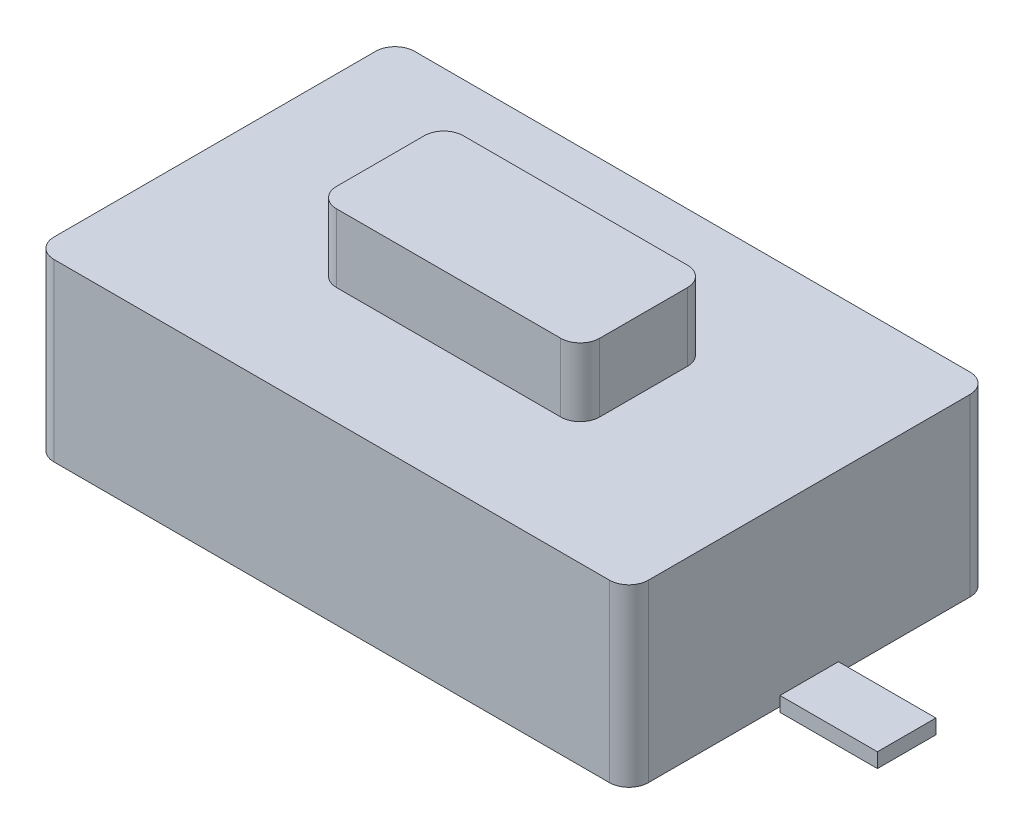
SolidWorks part; units mm, degrees
ref_plane "Спереди" through (0, 0, 0) normal (0, 0, 1) x (1, 0, 0)
ref_plane "Сверху" through (0, 0, 0) normal (0, 1, 0) x (1, 0, 0)
ref_plane "Справа" through (0, 0, 0) normal (1, 0, 0) x (0, 0, -1)
other "Configuration Table"
sketch "Эскиз1" plane through (0, 0, 0) normal (0, 1, 0) x (1, 0, 0)
  line L1 (-3.05, -1.85) -> (3.05, -1.85)
  line L2 (-3.05, -1.85) -> (-3.05, 1.85)
  line L3 (-3.05, 1.85) -> (3.05, 1.85)
  line L4 (3.05, -1.85) -> (3.05, 1.85)
  line L5 (-3.05, -1.85) -> (3.05, 1.85) construction
  line L6 (-3.05, 1.85) -> (3.05, -1.85) construction
  point P0 (0, 0)
  dimension "D1" = 6.1
  dimension "D2" = 3.7
extrude "Бобышка-Вытянуть1" add sketch "Эскиз1" along normal blind 1.8
sketch "Эскиз3" plane through (0, 1.8, 0) normal (0, 1, 0) x (1, 0, 0)
  line L1 (-1.35, -0.65) -> (1.35, -0.65)
  line L2 (-1.35, -0.65) -> (-1.35, 0.65)
  line L3 (-1.35, 0.65) -> (1.35, 0.65)
  line L4 (1.35, -0.65) -> (1.35, 0.65)
  line L5 (-1.35, -0.65) -> (1.35, 0.65) construction
  line L6 (-1.35, 0.65) -> (1.35, -0.65) construction
  point P0 (0, 0)
  dimension "D1" = 2.7
  dimension "D2" = 1.3
extrude "Бобышка-Вытянуть2" add sketch "Эскиз3" along normal blind 0.7
sketch "Эскиз4" plane through (0, 0, 0) normal (0, -1, 0) x (1, 0, 0)
  line L0 (-3.05, -1.85) -> (-3.05, 1.85) construction
  line L1 (-3.05, 0.3) -> (-4.05, 0.3)
  line L2 (-3.05, 0.3) -> (-3.05, -0.3)
  line L3 (-3.05, -0.3) -> (-4.05, -0.3)
  line L4 (-4.05, 0.3) -> (-4.05, -0.3)
  line L5 (-5.3832, 0) -> (4.6777, 0) construction
  dimension "D1" = 1
  dimension "D2" = 0.6
extrude "Бобышка-Вытянуть3" add sketch "Эскиз4" against normal blind 0.1 and the other way blind 0.05
mirror "Зеркальное отражение1" about plane through (0, 0, 0) normal (1, 0, 0) of "Бобышка-Вытянуть3"
fillet "Скругление1" radius 0.2 4 edges at (1.35, 2.15, 0.65) (-1.35, 2.15, 0.65) (1.35, 2.15, -0.65) (-1.35, 2.15, -0.65)
fillet "Скругление2" radius 0.2 4 edges at (3.05, 0.9, 1.85) (3.05, 0.9, -1.85) (-3.05, 0.9, -1.85) (-3.05, 0.9, 1.85)
